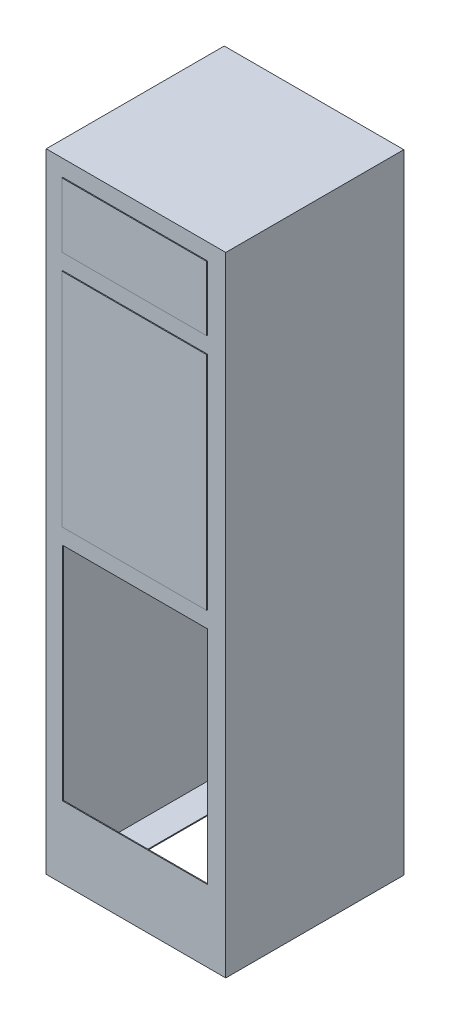
SolidWorks part; units mm, degrees
ref_plane "Alzado" through (0, 0, 0) normal (0, 0, 1) x (1, 0, 0)
ref_plane "Planta" through (0, 0, 0) normal (0, 1, 0) x (1, 0, 0)
ref_plane "Vista lateral" through (0, 0, 0) normal (1, 0, 0) x (0, 0, -1)
sketch "Croquis1" plane through (0, 0, 0) normal (0, 0, 1) x (1, 0, 0)
  line L1 (-300, -1050) -> (300, -1050)
  line L2 (-300, -1050) -> (-300, 1050)
  line L3 (-300, 1050) -> (300, 1050)
  line L4 (300, -1050) -> (300, 1050)
  line L5 (-300, -1050) -> (300, 1050) construction
  line L6 (-300, 1050) -> (300, -1050) construction
  point P0 (0, 0)
  dimension "D1" = 2100
  dimension "D2" = 600
extrude "Saliente-Extruir1" add sketch "Croquis1" along normal blind 595
sketch "Croquis2" plane through (0, 0, 595) normal (0, 0, 1) x (1, 0, 0)
  line L0 (300, -1050) -> (300, 1050) construction
  line L1 (-297, -1047) -> (297, -1047)
  line L2 (-297, -1047) -> (-297, 1047)
  line L3 (-297, 1047) -> (297, 1047)
  line L4 (297, -1047) -> (297, 1047)
  line L5 (-297, -1047) -> (297, 1047) construction
  line L6 (-297, 1047) -> (297, -1047) construction
  line L7 (300, 1050) -> (-300, 1050) construction
  point P0 (0, 0)
  dimension "D1" = 3
  dimension "D2" = 3
extrude "Cortar-Extruir1" cut sketch "Croquis2" against normal blind 592
sketch "Croquis3" plane through (0, 0, 595) normal (0, 0, 1) x (1, 0, 0)
  line L0 (-297, -1047) -> (-297, -810)
  line L1 (-297, 1047) -> (-297, -1047) construction
  line L2 (-297, -810) -> (297, -810)
  line L4 (297, -1047) -> (297, -810)
  line L5 (297, -1047) -> (297, 1047) construction
  line L6 (297, -1047) -> (-297, -1047)
  dimension "D1" = 237
extrude "Saliente-Extruir2" add sketch "Croquis3" against normal blind 3
sketch "Croquis4" plane through (0, -1050, 0) normal (0, -1, 0) x (1, 0, 0)
  line L0 (-300, 0) -> (300, 0) construction
  line L1 (-200, 495) -> (200, 495)
  line L2 (-200, 495) -> (-200, 100)
  line L3 (-200, 100) -> (200, 100)
  line L4 (200, 495) -> (200, 100)
  line L5 (-200, 495) -> (200, 100) construction
  line L6 (-200, 100) -> (200, 495) construction
  line L7 (300, 595) -> (300, 0) construction
  line L8 (-300, 595) -> (300, 595) construction
  line L9 (-300, 595) -> (-300, 0) construction
  point P0 (0, 297.5)
  point P11 (0, 495)
  dimension "D1" = 100
  dimension "D2" = 100
  dimension "D3" = 100
  dimension "D4" = 100
extrude "Cortar-Extruir2" cut sketch "Croquis4" against normal blind 3
sketch "Croquis5" plane through (0, 0, 595) normal (0, 0, 1) x (1, 0, 0)
  line L0 (-297, -810) -> (-297, -70)
  line L1 (-297, 1047) -> (-297, -810) construction
  line L2 (-297, -70) -> (-245, -70)
  line L3 (297, -810) -> (297, 1047) construction
  line L4 (297, -70) -> (297, -810)
  line L5 (297, -810) -> (239, -810)
  line L6 (-245, -70) -> (-245, -810)
  line L7 (-300, 1050) -> (-300, -1050) construction
  line L8 (239, -70) -> (239, -810)
  line L9 (-245, -810) -> (-297, -810)
  line L10 (239, -70) -> (297, -70)
  dimension "D1" = 740
  dimension "D2" = 55
  dimension "D3" = 58
extrude "Saliente-Extruir3" add sketch "Croquis5" against normal blind 3 separate body
sketch "Croquis6" plane through (0, 0, 595) normal (0, 0, 1) x (1, 0, 0)
  line L0 (-245, -810) -> (239, -810)
  line L1 (239, -810) -> (239, -70)
  line L2 (239, -70) -> (-245, -70)
  line L3 (-245, -70) -> (-245, -810)
extrude "Saliente-Extruir4" add sketch "Croquis6" along normal blind 3
sketch "Croquis7" plane through (0, 0, 595) normal (0, 0, 1) x (1, 0, 0)
  line L0 (-297, -70) -> (-297, -15)
  line L1 (-297, 1047) -> (-297, -1047) construction
  line L2 (-297, -15) -> (297, -15)
  line L3 (297, -1047) -> (297, 1047) construction
  line L4 (297, -15) -> (297, -70)
  line L5 (297, -70) -> (-297, -70)
  dimension "D1" = 55
extrude "Saliente-Extruir5" add sketch "Croquis7" against normal blind 3
sketch "Croquis8" plane through (0, 0, 595) normal (0, 0, 1) x (1, 0, 0)
  line L0 (-245, -15) -> (-245, 725)
  line L1 (297, -15) -> (-297, -15) construction
  line L2 (-245, 725) -> (-297, 725)
  line L3 (-297, 1047) -> (-297, -1047) construction
  line L4 (-297, 725) -> (-297, -15)
  line L5 (-297, -15) -> (-245, -15)
  line L6 (239, -15) -> (239, 725)
  line L7 (239, 725) -> (297, 725)
  line L8 (297, -15) -> (297, 1047) construction
  line L9 (297, 725) -> (297, -15)
  line L10 (297, -15) -> (239, -15)
  dimension "D1" = 740
extrude "Saliente-Extruir6" add sketch "Croquis8" against normal blind 3
sketch "Croquis9" plane through (0, 0, 595) normal (0, 0, 1) x (1, 0, 0)
  line L0 (-245, -15) -> (-245, 725)
  line L1 (-245, 725) -> (239, 725)
  line L2 (239, 725) -> (239, -15)
  line L3 (239, -15) -> (-245, -15)
extrude "Saliente-Extruir7" add sketch "Croquis9" along normal blind 3 separate body
sketch "Croquis10" plane through (0, 0, 595) normal (0, 0, 1) x (1, 0, 0)
  line L0 (-245, 780) -> (-245, 995)
  line L2 (239, 780) -> (239, 995)
  line L3 (-245, 995) -> (239, 995)
  line L4 (-245, 780) -> (239, 780)
  line L5 (300, 1050) -> (-300, 1050) construction
  line L6 (-245, 725) -> (-297, 725) construction
  line L7 (-297, 1047) -> (297, 1047)
  line L8 (297, 1047) -> (297, 725)
  line L9 (297, 725) -> (-297, 725)
  line L10 (-297, 725) -> (-297, 1047)
  dimension "D1" = 55
  dimension "D2" = 55
extrude "Saliente-Extruir8" add sketch "Croquis10" against normal blind 3
sketch "Croquis11" plane through (0, 0, 595) normal (0, 0, 1) x (1, 0, 0)
  line L0 (-245, 995) -> (239, 995)
  line L1 (239, 995) -> (239, 780)
  line L2 (239, 780) -> (-245, 780)
  line L3 (-245, 780) -> (-245, 995)
extrude "Saliente-Extruir9" add sketch "Croquis11" along normal blind 3 separate body
sketch "Croquis12" plane through (0, 0, 598) normal (0, 0, 1) x (1, 0, 0)
  line L0 (-245, -810) -> (-245, -70)
  line L1 (-245, -70) -> (239, -70)
  line L2 (239, -70) -> (239, -810)
  line L3 (239, -810) -> (-245, -810)
extrude "Cortar-Extruir3" cut sketch "Croquis12" against normal blind 4
